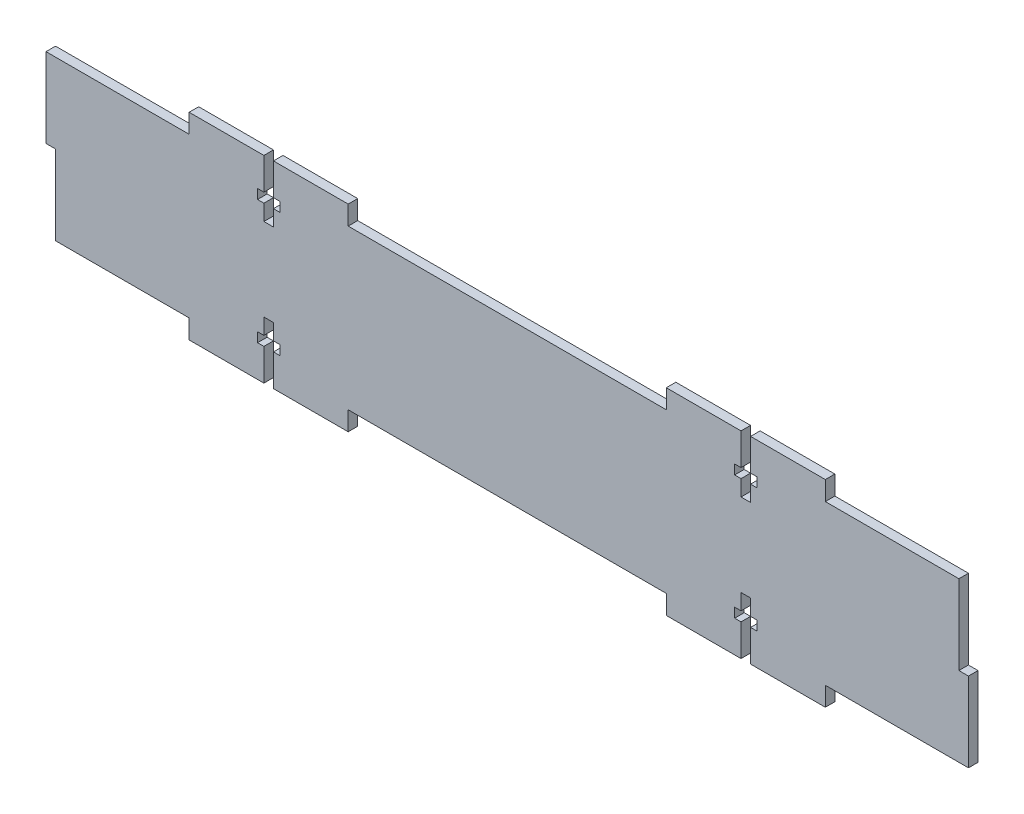
SolidWorks part; units mm, degrees
ref_plane "Front Plane" through (0, 0, 0) normal (0, 0, 1) x (1, 0, 0)
ref_plane "Top Plane" through (0, 0, 0) normal (0, 1, 0) x (1, 0, 0)
ref_plane "Right Plane" through (0, 0, 0) normal (1, 0, 0) x (0, 0, -1)
sketch "Sketch1" plane through (0, 0, 0) normal (0, 0, 1) x (1, 0, 0)
  line L0 (-145, 0) -> (-142, 0)
  line L1 (-145, 25) -> (-100, 25)
  line L2 (-145, 25) -> (-145, 0)
  line L3 (-142, -25) -> (-100, -25)
  line L4 (145, 0) -> (145, -25)
  line L5 (-145, 25) -> (145, -25) construction
  line L6 (-142, -24.4828) -> (142, 24.4828) construction
  line L7 (-142, 0) -> (-142, -25)
  line L8 (145, 0) -> (142, 0)
  line L9 (142, 0) -> (142, 25)
  line L10 (-145, 25) -> (-145, 44.7312) construction
  line L11 (-145, 44.7312) -> (-100, 44.7312) construction
  line L12 (-100, 44.7312) -> (-100, 56.9469) construction
  line L13 (-100, 56.9469) -> (-50, 56.9469) construction
  line L14 (-50, 56.9469) -> (-50, 44.7312) construction
  line L15 (-50, 44.7312) -> (50, 44.7312) construction
  line L16 (50, 44.7312) -> (50, 56.9469) construction
  line L17 (50, 56.9469) -> (100, 56.9469) construction
  line L18 (100, 56.9469) -> (100, 44.7312) construction
  line L19 (100, 44.7312) -> (145, 44.7312) construction
  line L20 (-100, 25) -> (-100, 31)
  line L21 (-100, 31) -> (-50, 31)
  line L22 (-50, 31) -> (-50, 25)
  line L23 (50, 25) -> (50, 31)
  line L24 (50, 31) -> (100, 31)
  line L25 (100, 31) -> (100, 25)
  line L26 (-100, -25) -> (-100, -31)
  line L27 (-100, -31) -> (-50, -31)
  line L28 (-50, -31) -> (-50, -25)
  line L29 (50, -25) -> (50, -31)
  line L30 (50, -31) -> (100, -31)
  line L31 (100, -31) -> (100, -25)
  line L32 (-50, 25) -> (50, 25)
  line L33 (-50, -25) -> (50, -25)
  line L34 (100, -25) -> (145, -25)
  line L35 (100, 25) -> (142, 25)
  line L36 (100, 25) -> (100, -25) construction
  line L37 (100, 0) -> (145, 0) construction
  line L38 (-100, 25) -> (-100, -25) construction
  line L39 (-100, 0) -> (-145, 0) construction
  line L40 (122.5, 25) -> (122.5, 19) construction
  line L41 (122.5, -25) -> (122.5, -19) construction
  point P0 (0, 0)
extrude "Boss-Extrude1" add sketch "Sketch1" along normal blind 3
sketch "Sketch2" plane through (0, 0, 3) normal (0, 0, 1) x (1, 0, 0)
  line L0 (-100, 31) -> (-75, 31) construction
  line L1 (-50, 31) -> (-100, 31) construction
  line L2 (-75, 31) -> (-75, 21) construction
  line L3 (-75, 31) -> (-76.5, 31)
  line L4 (-76.5, 31) -> (-76.5, 21)
  line L5 (-76.5, 21) -> (-78.5, 21)
  line L6 (-78.5, 21) -> (-78.5, 18)
  line L7 (-78.5, 18) -> (-76.5, 18)
  line L8 (-71.5, 18) -> (-71.5, 21)
  line L9 (-71.5, 21) -> (-73.5, 21)
  line L10 (-73.5, 21) -> (-73.5, 31)
  line L11 (-73.5, 31) -> (-75, 31)
  line L12 (-76.5, 18) -> (-76.5, 13)
  line L13 (-76.5, 13) -> (-73.5, 13)
  line L14 (-73.5, 13) -> (-73.5, 18)
  line L15 (-73.5, 18) -> (-71.5, 18)
  line L16 (-76.5, -31) -> (-76.5, -21)
  line L18 (-100, -31) -> (-50, -31) construction
  line L19 (-76.5, -21) -> (-78.5, -21)
  line L20 (-78.5, -21) -> (-78.5, -18)
  line L21 (-78.5, -18) -> (-76.5, -18)
  line L22 (-76.5, -18) -> (-76.5, -13)
  line L23 (-76.5, -13) -> (-73.5, -13)
  line L24 (-73.5, -13) -> (-73.5, -18)
  line L25 (-73.5, -18) -> (-71.5, -18)
  line L26 (-71.5, -18) -> (-71.5, -21)
  line L27 (-71.5, -21) -> (-73.5, -21)
  line L28 (-73.5, -21) -> (-73.5, -31)
  line L29 (-73.5, -31) -> (-76.5, -31)
  line L30 (75, 31) -> (75, 13) construction
  line L31 (100, 31) -> (50, 31) construction
  line L33 (73.5, 31) -> (73.5, 21)
  line L34 (73.5, 21) -> (71.5, 21)
  line L35 (71.5, 21) -> (71.5, 18)
  line L36 (71.5, 18) -> (73.5, 18)
  line L37 (73.5, 18) -> (73.5, 13)
  line L38 (73.5, 13) -> (76.5, 13)
  line L39 (76.5, 13) -> (76.5, 18)
  line L40 (76.5, 18) -> (78.5, 18)
  line L41 (78.5, 18) -> (78.5, 21)
  line L42 (78.5, 21) -> (76.5, 21)
  line L43 (76.5, 21) -> (76.5, 31)
  line L44 (76.5, 31) -> (73.5, 31)
  line L45 (73.5, -31) -> (73.5, -21)
  line L46 (50, -31) -> (100, -31) construction
  line L47 (73.5, -21) -> (71.5, -21)
  line L48 (71.5, -21) -> (71.5, -18)
  line L49 (71.5, -18) -> (73.5, -18)
  line L50 (73.5, -18) -> (73.5, -13)
  line L51 (73.5, -13) -> (76.5, -13)
  line L52 (76.5, -13) -> (76.5, -18)
  line L53 (76.5, -18) -> (78.5, -18)
  line L54 (78.5, -18) -> (78.5, -21)
  line L55 (78.5, -21) -> (76.5, -21)
  line L56 (76.5, -21) -> (76.5, -31)
  line L57 (76.5, -31) -> (73.5, -31)
extrude "Cut-Extrude1" cut sketch "Sketch2" against normal blind 10
